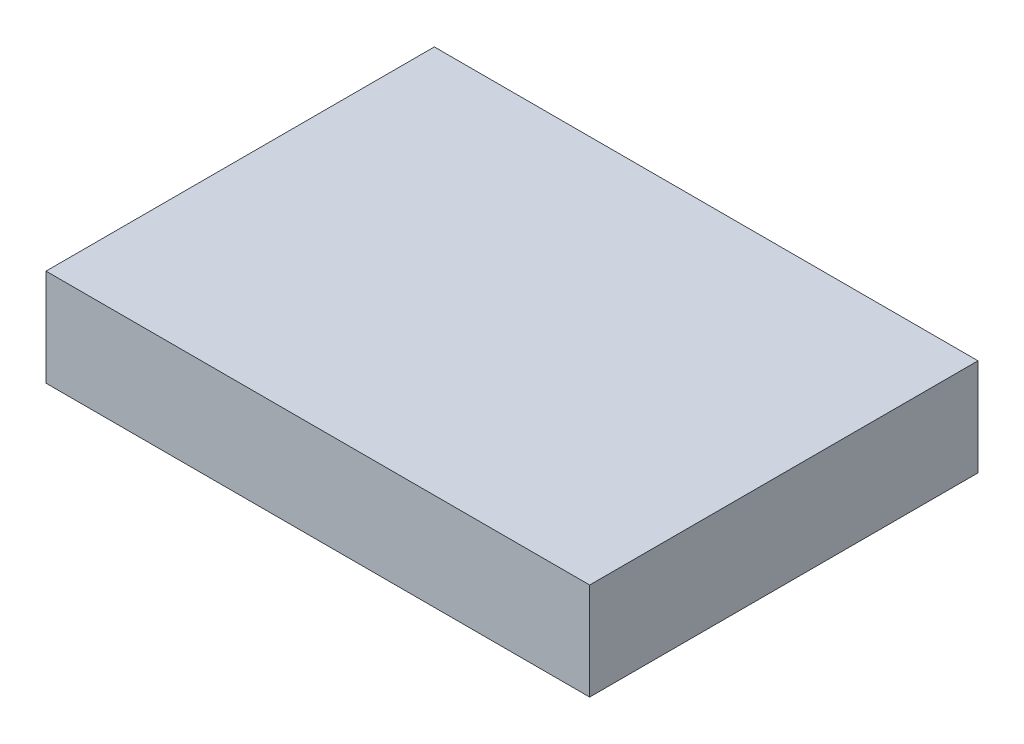
SolidWorks part; units mm, degrees
ref_plane "Front Plane" through (0, 0, 0) normal (0, 0, 1) x (1, 0, 0)
ref_plane "Top Plane" through (0, 0, 0) normal (0, 1, 0) x (1, 0, 0)
ref_plane "Right Plane" through (0, 0, 0) normal (1, 0, 0) x (0, 0, -1)
sketch "Sketch1" plane through (0, 0, 0) normal (0, 1, 0) x (1, 0, 0)
  line L1 (-88.9, -63.5) -> (88.9, -63.5)
  line L2 (-88.9, -63.5) -> (-88.9, 63.5)
  line L3 (-88.9, 63.5) -> (88.9, 63.5)
  line L4 (88.9, -63.5) -> (88.9, 63.5)
  line L5 (-88.9, -63.5) -> (88.9, 63.5) construction
  line L6 (-88.9, 63.5) -> (88.9, -63.5) construction
  point P0 (0, 0)
  dimension "D1" = 177.8
  dimension "D2" = 127
extrude "Boss-Extrude1" add sketch "Sketch1" along normal blind 31.75
